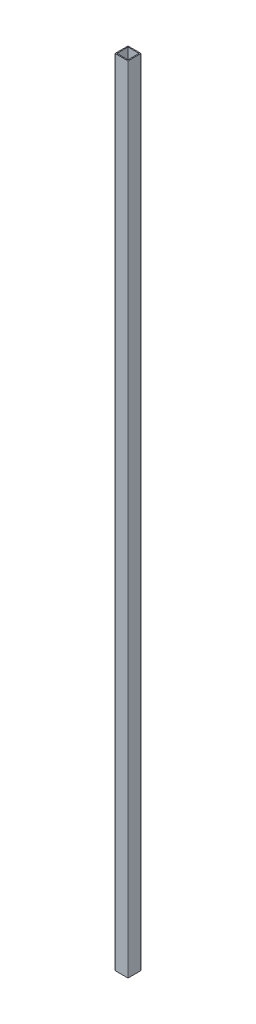
SolidWorks part; units mm, degrees
ref_plane "Front Plane" through (0, 0, 0) normal (0, 0, 1) x (1, 0, 0)
ref_plane "Top Plane" through (0, 0, 0) normal (0, 1, 0) x (1, 0, 0)
ref_plane "Right Plane" through (0, 0, 0) normal (1, 0, 0) x (0, 0, -1)
sketch "Sketch1" plane through (0, 0, 0) normal (0, 1, 0) x (1, 0, 0)
  line L0 (1.5, 1.5) -> (18.5, 1.5)
  line L1 (0.5, 0) -> (19.5, 0)
  line L2 (0, 0.5) -> (0, 19.5)
  line L3 (0.5, 20) -> (19.5, 20)
  line L4 (20, 0.5) -> (20, 19.5)
  line L5 (18.5, 1.5) -> (18.5, 18.5)
  line L6 (1.5, 18.5) -> (18.5, 18.5)
  line L7 (1.5, 1.5) -> (1.5, 18.5)
  arc A0 (19.5, 0) -> (20, 0.5) centre (19.5, 0.5) ccw
  arc A1 (0.5, 0) -> (0, 0.5) centre (0.5, 0.5) cw
  arc A2 (0, 19.5) -> (0.5, 20) centre (0.5, 19.5) cw
  arc A3 (19.5, 20) -> (20, 19.5) centre (19.5, 19.5) cw
  arc A4 (18.5, 1.5) -> (18.5, 1.5) centre (18.5, 1.5) ccw
  arc A5 (18.5, 18.5) -> (18.5, 18.5) centre (18.5, 18.5) cw
  arc A6 (1.5, 18.5) -> (1.5, 18.5) centre (1.5, 18.5) cw
  arc A7 (1.5, 1.5) -> (1.5, 1.5) centre (1.5, 1.5) cw
  point P9 (0, 0)
  dimension "D3" = 0.5
  dimension "D1" = 20
  dimension "D2" = 20
  dimension "D4" = 1.5
extrude "Boss-Extrude1" add sketch "Sketch1" along normal blind 1220
sketch "Sketch5" plane through (0, 0, 0) normal (-1, 0, 0) x (0, 0, 1)
  line L0 (0, 1220) -> (0, 0) construction
  line L1 (0, 1033.5) -> (-5, 1033.5)
  line L2 (0, 1033.5) -> (0, 1013.5)
  line L3 (0, 1013.5) -> (-5, 1013.5)
  line L4 (-5, 1033.5) -> (-5, 1013.5)
  line L5 (-19.5, 1220) -> (-0.5, 1220) construction
  line L6 (0, 843.5) -> (-5, 843.5)
  line L7 (0, 843.5) -> (0, 823.5)
  line L8 (0, 823.5) -> (-5, 823.5)
  line L9 (-5, 843.5) -> (-5, 823.5)
  line L10 (0, 653.5) -> (-5, 653.5)
  line L11 (0, 653.5) -> (0, 633.5)
  line L12 (0, 633.5) -> (-5, 633.5)
  line L13 (-5, 653.5) -> (-5, 633.5)
  line L14 (0, 463.5) -> (-5, 463.5)
  line L15 (0, 463.5) -> (0, 443.5)
  line L16 (0, 443.5) -> (-5, 443.5)
  line L17 (-5, 463.5) -> (-5, 443.5)
  dimension "D1" = 186.5
  dimension "D2" = 20
  dimension "D3" = 5
  dimension "D4" = 4
extrude "Cut-Extrude2" [suppressed] cut sketch "Sketch5" against normal through all
sketch "Sketch6" plane through (0, 0, 0) normal (0, 0, 1) x (1, 0, 0)
  line L0 (0.5, 1220) -> (19.5, 1220) construction
  line L1 (4, 1205) -> (16, 1205)
  line L2 (4, 1205) -> (4, 1201)
  line L3 (4, 1201) -> (16, 1201)
  line L4 (16, 1205) -> (16, 1201)
  line L5 (10, 1205) -> (10, 1220) construction
  line L6 (19.5, 610) -> (0.5, 610) construction
  line L7 (19.5, 1220) -> (19.5, 0) construction
  line L8 (0.5, 1220) -> (0.5, 0) construction
  line L9 (16, 15) -> (16, 19)
  line L10 (4, 19) -> (16, 19)
  line L11 (4, 15) -> (4, 19)
  line L12 (4, 15) -> (16, 15)
  dimension "D1" = 15
  dimension "D2" = 12
  dimension "D3" = 4
extrude "Cut-Extrude3" [suppressed] cut sketch "Sketch6" against normal blind 10
